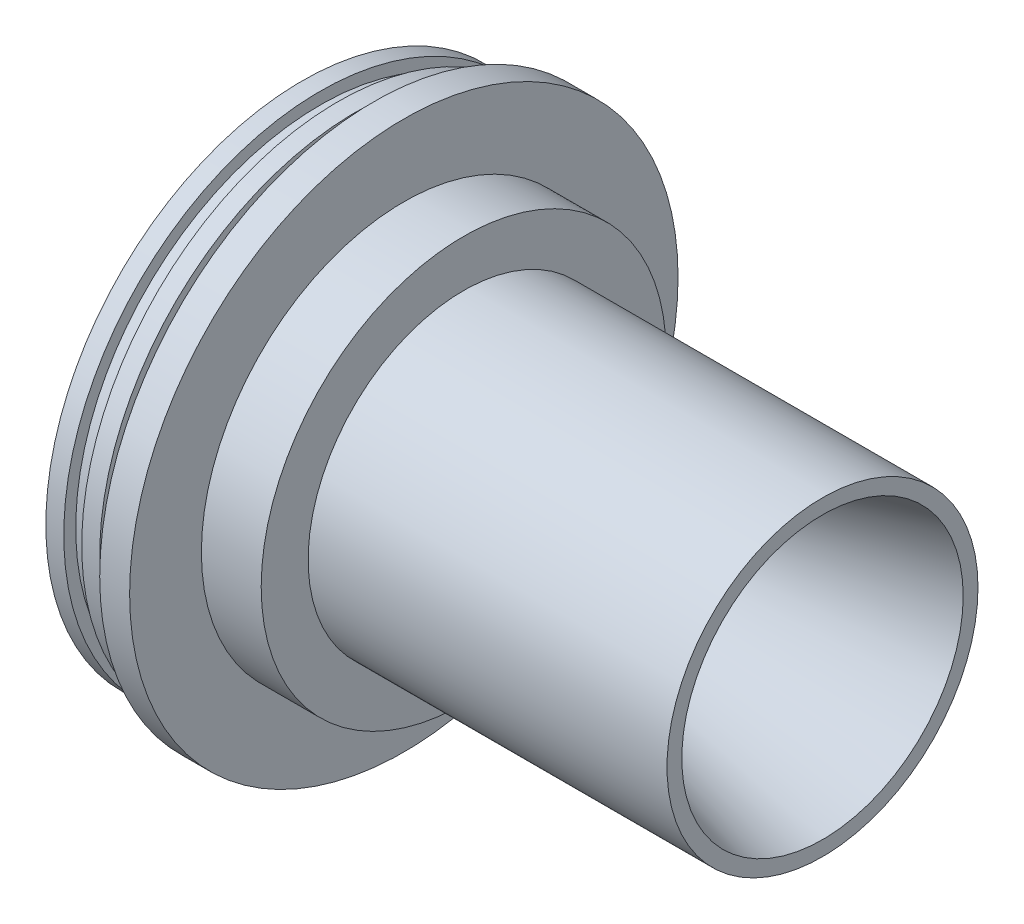
SolidWorks part; units mm, degrees
material "C (Graphite)"
ref_plane "Ebene vorne" through (0, 0, 0) normal (0, 0, 1) x (1, 0, 0)
ref_plane "Ebene oben" through (0, 0, 0) normal (0, 1, 0) x (1, 0, 0)
ref_plane "Ebene rechts" through (0, 0, 0) normal (1, 0, 0) x (0, 0, -1)
sketch "Sketch1" plane through (0, 0, 0) normal (0, 0, 1) x (1, 0, 0)
  line L0 (-87, 41.0806) -> (-60.8928, 14.9734)
  line L1 (-46.4039, 11.0911) -> (0, 23.525)
  line L2 (0, 23.525) -> (0, 26)
  line L3 (0, 26) -> (-60, 26)
  line L7 (-70, 45.85) -> (-75, 45.85)
  line L8 (-75, 45.85) -> (-75, 40.86)
  line L9 (-75, 40.86) -> (-78, 40.86)
  line L10 (-78, 40.86) -> (-78, 42.86)
  line L11 (-78, 42.86) -> (-81, 42.86)
  line L12 (-81, 42.86) -> (-81, 40.86)
  line L13 (-81, 40.86) -> (-84, 40.86)
  line L14 (-84, 40.86) -> (-84, 42.86)
  line L15 (-84, 42.86) -> (-87, 42.86)
  line L16 (-87, 42.86) -> (-87, 41.0806)
  line L17 (0, 0) -> (-121.2218, 0) construction
  line L18 (-70, 45.85) -> (-70, 33.85)
  line L19 (-70, 33.85) -> (-60, 33.85)
  line L20 (-60, 33.85) -> (-60, 26)
  arc A0 (-60.8928, 14.9734) -> (-46.4039, 11.0911) centre (-50.2862, 25.58) ccw
  circle A1 centre (-60, 26) radius 8.4283 construction
  dimension "D10" = 15
  dimension "D1" = 45
  dimension "D2" = 15
  dimension "D3" = 26
  dimension "D5" = 3
  dimension "D6" = 3
  dimension "D7" = 3
  dimension "D8" = 2
  dimension "D9" = 3
  dimension "D11" = 25.58
  dimension "D12" = 23.525
  dimension "D13" = 5
  dimension "D14" = 10
  dimension "D15" = 60
  dimension "D4" = 42.86
  dimension "D16" = 45.85
  dimension "D17" = 12
revolve "Revolve1" add sketch "Sketch1" angle 360 about L17
equation "\"D7@Sketch1\"=\"D5@Sketch1\""
